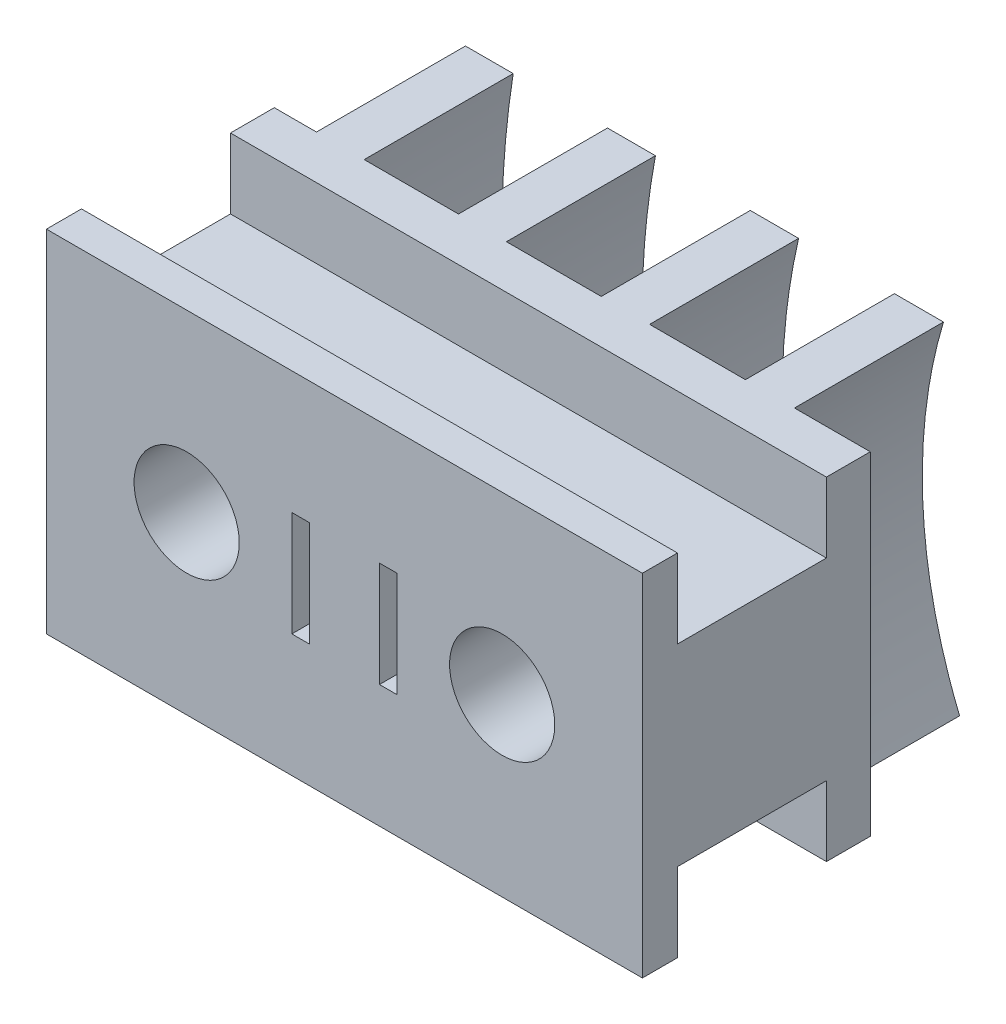
SolidWorks part; units mm, degrees
ref_plane "Plan de face" through (0, 0, 0) normal (0, 0, 1) x (1, 0, 0)
ref_plane "Plan de dessus" through (0, 0, 0) normal (0, 1, 0) x (1, 0, 0)
ref_plane "Plan de droite" through (0, 0, 0) normal (1, 0, 0) x (0, 0, -1)
sketch "Esquisse1" plane through (0, 0, 0) normal (0, 0, 1) x (1, 0, 0)
  line L1 (11.5, -2.75) -> (28.5, -2.75)
  line L2 (11.5, -2.75) -> (11.5, 2.75)
  line L3 (11.5, 2.75) -> (28.5, 2.75)
  line L4 (28.5, -2.75) -> (28.5, 2.75)
  line L5 (7.4162, -3) -> (39.8873, -3) construction
  line L6 (7.4162, 3) -> (39.8873, 3) construction
  arc A1 (6.245, -5) -> (6.245, 5) centre (0, 0) ccw construction
  dimension "D4" = 11.5
  dimension "D1" = 17
  dimension "D2" = 0.25
  dimension "D3" = 0.25
extrude "Boss.-Extru.1" add sketch "Esquisse1" against normal blind 5.5
sketch "Esquisse2" plane through (28.5, 0, 0) normal (1, 0, 0) x (0, 0, -1)
  line L0 (5.5, -2.75) -> (5.5, 2.75) construction
  line L1 (4.25, -4.75) -> (5.5, -4.75)
  line L2 (4.25, -4.75) -> (4.25, 4.75)
  line L3 (4.25, 4.75) -> (5.5, 4.75)
  line L4 (5.5, -4.75) -> (5.5, 4.75)
  line L5 (4, -5) -> (4, -3) construction
  line L6 (10, -5) -> (4, -5) construction
  line L7 (4, 5) -> (10, 5) construction
  dimension "D1" = 0.25
  dimension "D2" = 0.25
  dimension "D3" = 0.25
extrude "Boss.-Extru.2" add sketch "Esquisse2" against normal up to vertex (17 mm away)
sketch "Esquisse3" plane through (0, 0, 0) normal (0, 0, 1) x (1, 0, 0)
  line L0 (11.5, 2.75) -> (11.5, -2.75) construction
  line L1 (28.5, -5) -> (11.5, -5)
  line L2 (28.5, -5) -> (28.5, 5)
  line L3 (28.5, 5) -> (11.5, 5)
  line L4 (11.5, -5) -> (11.5, 5)
  line L5 (28.5, -2.75) -> (28.5, 2.75) construction
  point P8 (11.5, 0)
  point P9 (11.5, 0)
  dimension "D1" = 10
extrude "Boss.-Extru.3" add sketch "Esquisse3" along normal blind 1
sketch "Esquisse4" plane through (0, 0, 1) normal (0, 0, 1) x (1, 0, 0)
  line L0 (28.5, 0) -> (11.5, 0) construction
  line L1 (28.5, -5) -> (28.5, 5) construction
  line L2 (11.5, 5) -> (11.5, -5) construction
  circle A0 centre (24.5, 0) radius 1.5
  circle A1 centre (15.5, 0) radius 1.5
  point P11 (15.5, 0)
  point P13 (24.5, 0)
  dimension "D1" = 3
  dimension "D2" = 3
  dimension "D3" = 4
  dimension "D4" = 4
extrude "Enlèv. mat.-Extru.1" cut sketch "Esquisse4" against normal blind 3.5
sketch "Esquisse5" plane through (0, 0, 1) normal (0, 0, 1) x (1, 0, 0)
  line L0 (11.5, -5) -> (28.5, -5) construction
  line L1 (21.5, -1.5) -> (21, -1.5)
  line L2 (21.5, -1.5) -> (21.5, 1.5)
  line L3 (21.5, 1.5) -> (21, 1.5)
  line L4 (21, -1.5) -> (21, 1.5)
  line L5 (19, -1.5) -> (18.5, -1.5)
  line L6 (19, -1.5) -> (19, 1.5)
  line L7 (19, 1.5) -> (18.5, 1.5)
  line L8 (18.5, -1.5) -> (18.5, 1.5)
  line L9 (28.5, -5) -> (28.5, 5) construction
  line L10 (11.5, 5) -> (11.5, -5) construction
  dimension "D1" = 0.5
  dimension "D2" = 0.5
  dimension "D3" = 3.5
  dimension "D4" = 3.5
  dimension "D5" = 7
  dimension "D6" = 7
  dimension "D7" = 3
  dimension "D8" = 3
extrude "Enlèv. mat.-Extru.2" cut sketch "Esquisse5" against normal blind 0.5
sketch "Esquisse6" plane through (0, 0, -5.5) normal (0, 0, -1) x (-1, 0, 0)
  line L0 (-22.5528, -4.75) -> (-21.1481, -4.75)
  line L1 (-24.9387, 4.75) -> (-26.3382, 4.75)
  line L2 (-20.827, 4.75) -> (-22.2056, 4.75)
  line L3 (-18.4019, -4.75) -> (-17.0169, -4.75)
  line L4 (-11.5, -4.75) -> (-11.5, 4.75)
  line L5 (-11.5, 4.75) -> (-28.5, 4.75)
  line L6 (-28.5, 4.75) -> (-28.5, -4.75)
  line L7 (-28.5, -4.75) -> (-11.5, -4.75)
  line L9 (-12.7026, 4.75) -> (-14.0645, 4.75)
  line L11 (-26.7976, -4.75) -> (-25.3526, -4.75)
  line L12 (-16.754, 4.75) -> (-18.1221, 4.75)
  line L13 (-14.3, -4.75) -> (-12.9262, -4.75)
  line L14 (-11.5, 4.75) -> (-11.5, -4.75) construction
  spline S0 degree 3 poles (-16.754, 4.75) (-16.6225, 4.0063) (-16.2154, 0.8256) (-16.4622, -2.3891) (-17.0169, -4.75) knots 0.375647 0.375647 0.375647 0.375647 0.377334 0.382815 0.382815 0.382815 0.382815
  spline S1 degree 3 poles (-26.7976, -4.75) (-26.3952, -3.7721) (-25.6729, -1.2498) (-25.6691, 2.034) (-26.1639, 4.1678) (-26.3382, 4.75) knots 0.135603 0.135603 0.135603 0.135603 0.139596 0.145401 0.147627 0.147627 0.147627 0.147627
  spline S4 degree 3 poles (-14.3, -4.75) (-13.8469, -2.5907) (-13.5863, 0.6053) (-13.9121, 3.7885) (-14.0645, 4.75) knots 0.471793 0.471793 0.471793 0.471793 0.47627 0.478228 0.478228 0.478228 0.478228
  spline S5 degree 3 poles (-20.827, 4.75) (-20.702, 4.1662) (-20.2473, 1.4455) (-20.3939, -1.7941) (-21.0213, -4.3089) (-21.1481, -4.75) knots 0.48603 0.48603 0.48603 0.48603 0.487632 0.493437 0.494689 0.494689 0.494689 0.494689
  spline S6 degree 3 poles (-24.9387, 4.75) (-24.7907, 4.2057) (-24.3086, 1.9651) (-24.3333, -1.3048) (-25.0246, -3.8646) (-25.3526, -4.75) knots 0.596037 0.596037 0.596037 0.596037 0.59793 0.603735 0.606985 0.606985 0.606985 0.606985
  spline S7 degree 3 poles (-12.7026, 4.75) (-12.5482, 3.7246) (-12.2495, 0.5415) (-12.5078, -2.6491) (-12.9262, -4.75) knots 0.265052 0.265052 0.265052 0.265052 0.267037 0.27117 0.27117 0.27117 0.27117
  spline S8 degree 3 poles (-18.4019, -4.75) (-18.3935, -4.7162) (-17.8029, -2.3327) (-17.5543, 0.8897) (-17.988, 4.0362) (-18.1221, 4.75) knots 0.360092 0.360092 0.360092 0.360092 0.360175 0.36598 0.3677 0.3677 0.3677 0.3677
  spline S9 degree 3 poles (-22.5528, -4.75) (-22.3736, -4.1733) (-21.729, -1.6635) (-21.6078, 1.5838) (-22.07, 4.1617) (-22.2056, 4.75) knots 0.248115 0.248115 0.248115 0.248115 0.249886 0.255691 0.257428 0.257428 0.257428 0.257428
  dimension "D1" = 1.2026
  dimension "D3" = 1.4262
  dimension "D4" = 2.5645
  dimension "D5" = 2.8
  dimension "D6" = 5.254
  dimension "D7" = 5.5169
  dimension "D8" = 6.6221
  dimension "D9" = 6.9019
  dimension "D10" = 9.327
  dimension "D11" = 9.6481
  dimension "D12" = 10.7056
  dimension "D13" = 11.0528
  dimension "D14" = 13.4387
  dimension "D15" = 13.8526
  dimension "D16" = 14.8382
  dimension "D17" = 15.2976
  dimension "D2" = 0
extrude "Boss.-Extru.4" add sketch "Esquisse6" along normal offset from surface (4.25 mm away) 0.25
